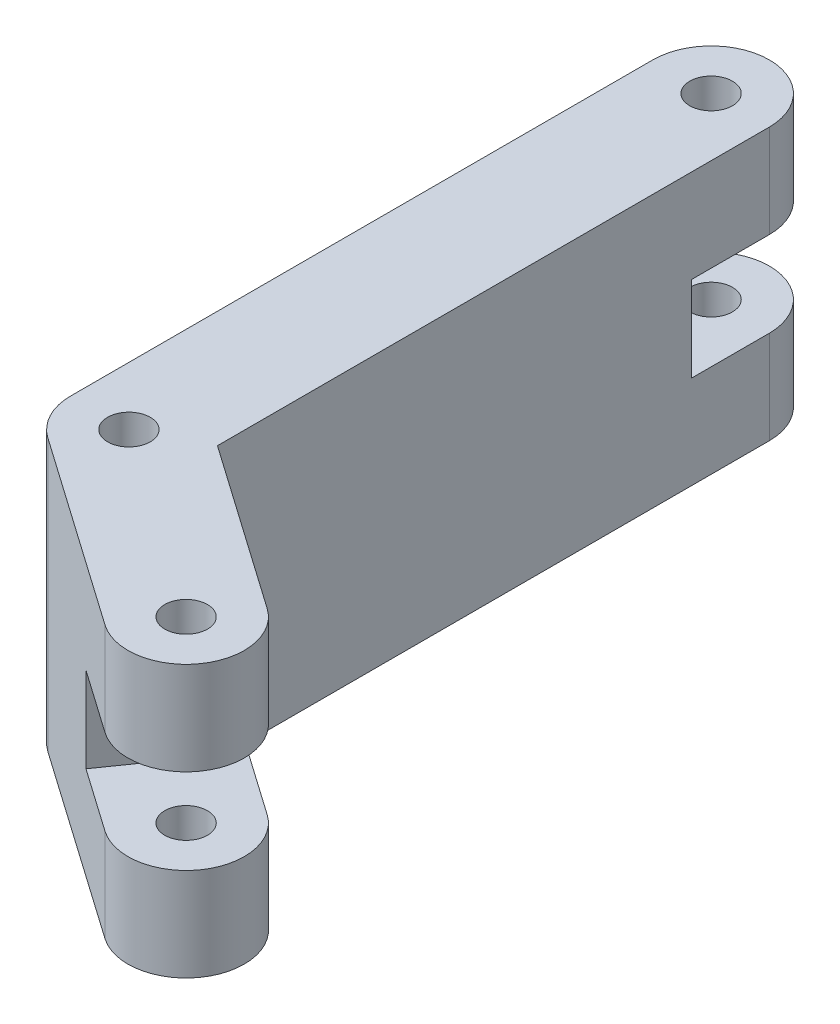
SolidWorks part; units mm, degrees
ref_plane "Front Plane" through (0, 0, 0) normal (0, 0, 1) x (1, 0, 0)
ref_plane "Top Plane" through (0, 0, 0) normal (0, 1, 0) x (1, 0, 0)
ref_plane "Right Plane" through (0, 0, 0) normal (1, 0, 0) x (0, 0, -1)
sketch "Sketch2" plane through (0, 0, 0) normal (0, 1, 0) x (1, 0, 0)
  line L0 (0, 0) -> (0, 75)
  line L1 (0, 0) -> (24.5746, -17.2073)
  line L2 (0, 75) -> (0, 0) construction
  line L3 (7.5, 75) -> (7.5, 0)
  line L4 (-7.5, 75) -> (-7.5, 0)
  line L5 (24.5746, -17.2073) -> (0, 0) construction
  line L6 (20.2727, -23.3509) -> (-4.3018, -6.1436)
  line L7 (28.8764, -11.0637) -> (4.3018, 6.1436)
  circle A0 centre (0, 75) radius 2.75
  circle A1 centre (0, 0) radius 2.75
  circle A2 centre (24.5746, -17.2073) radius 2.75
  arc A3 (7.5, 75) -> (-7.5, 75) centre (0, 75) ccw
  arc A4 (-7.5, 0) -> (7.5, 0) centre (0, 0) ccw
  arc A5 (20.2727, -23.3509) -> (28.8764, -11.0637) centre (24.5746, -17.2073) ccw
  arc A6 (4.3018, 6.1436) -> (-4.3018, -6.1436) centre (0, 0) ccw
  point P7 (0, 37.5)
  point P12 (12.2873, -8.6036)
extrude "Boss-Extrude2" add sketch "Sketch2" along normal blind 35
sketch "Sketch3" plane through (7.5, 0, 0) normal (1, 0, 0) x (0, 0, -1)
  line L0 (75, 17.5) -> (75, 23)
  line L1 (75, 35) -> (75, 0) construction
  line L2 (75, 17.5) -> (75, 12)
  line L3 (75, 12) -> (65, 12)
  line L4 (65, 12) -> (65, 23)
  line L5 (65, 23) -> (87.1832, 23)
  line L6 (87.1832, 23) -> (87.1832, 12)
  line L7 (87.1832, 12) -> (75, 12)
extrude "Cut-Extrude1" cut sketch "Sketch3" against normal blind 35 contours L3 L4 L5 L6 L7
sketch "Sketch4" plane through (4.3018, 0, -6.1436) normal (0.5736, 0, -0.8192) x (-0.8192, 0, -0.5736)
  line L0 (-30, 17.5) -> (-30, 12)
  line L1 (-30, 35) -> (-30, 0) construction
  line L2 (-30, 17.5) -> (-30, 23)
  line L3 (-30, 23) -> (-20, 23)
  line L4 (-20, 23) -> (-20, 12)
  line L5 (-20, 12) -> (-43.6303, 12)
  line L6 (-43.6303, 12) -> (-43.6303, 23)
  line L7 (-43.6303, 23) -> (-30, 23)
  line M4 (-30, 35) -> (-30, 0)
extrude "Cut-Extrude2" cut sketch "Sketch4" against normal blind 35 contours L7 L6 L5 M4 | L5 L4 L3 M4
